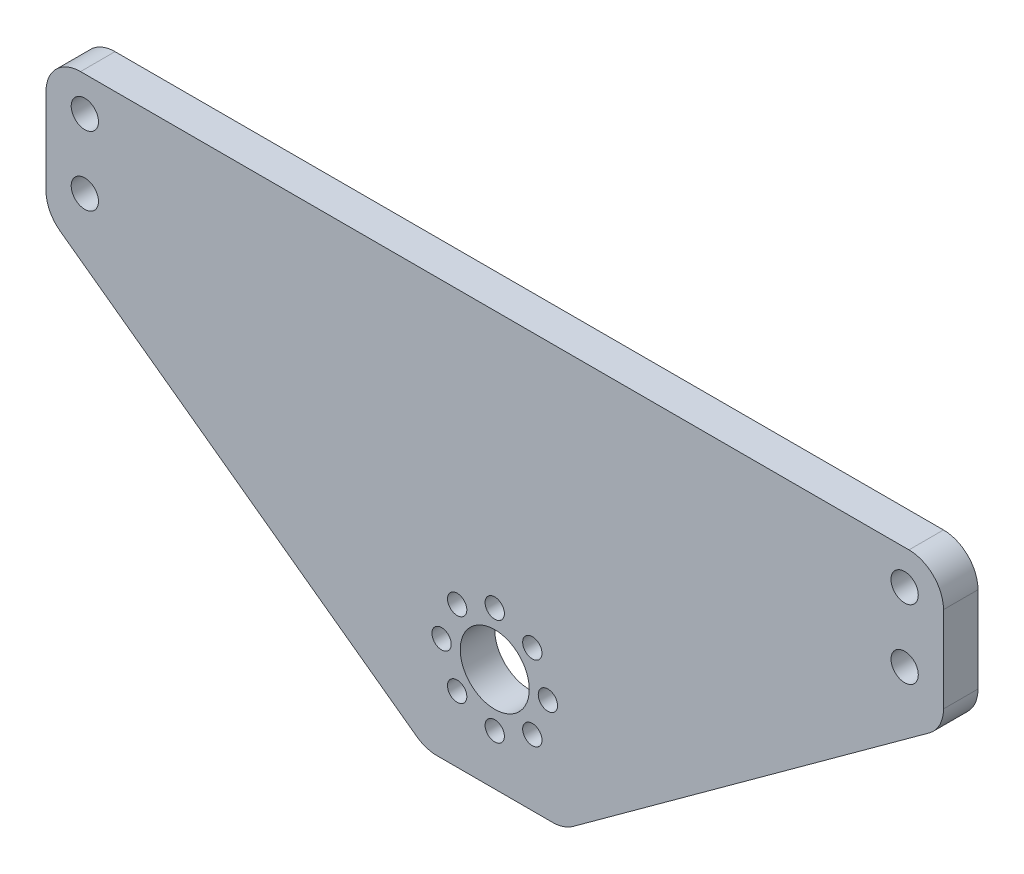
SolidWorks part; units mm, degrees
material "6061-T6 (SS)"
ref_plane "Front Plane" through (0, 0, 0) normal (0, 0, 1) x (1, 0, 0)
ref_plane "Top Plane" through (0, 0, 0) normal (0, 1, 0) x (1, 0, 0)
ref_plane "Right Plane" through (0, 0, 0) normal (1, 0, 0) x (0, 0, -1)
sketch "Sketch1" plane through (0, 0, 0) normal (0, 0, 1) x (1, 0, 0)
  line L1 (82.55, 38.1) -> (-82.55, 38.1)
  line L2 (82.55, 38.1) -> (82.55, -38.1)
  line L3 (82.55, -38.1) -> (-82.55, -38.1)
  line L4 (-82.55, 38.1) -> (-82.55, -38.1)
  line L5 (82.55, 38.1) -> (-82.55, -38.1) construction
  line L6 (82.55, -38.1) -> (-82.55, 38.1) construction
  circle A0 centre (0, -19.05) radius 6.35
  circle A1 centre (-75.4063, 31.75) radius 2.5083
  circle A2 centre (75.4062, 31.75) radius 2.5083
  circle A3 centre (75.4062, 19.05) radius 2.5083
  circle A4 centre (-75.4063, 19.05) radius 2.5083
  point P0 (0, 0)
  dimension "D3" = 12.7
  dimension "D4" = 75.4062
  dimension "D8" = 5.0165
  dimension "D9" = 5.0165
  dimension "D10" = 19.05
  dimension "D11" = 5.0165
  dimension "D12" = 5.0165
  dimension "D1" = 165.1
  dimension "D2" = 76.2
  dimension "D5" = 75.4062
  dimension "D6" = 50.8
  dimension "D7" = 50.8
  dimension "D13" = 75.4062
  dimension "D14" = 75.4063
  dimension "D15" = 12.7
  dimension "D16" = 12.7
extrude "Boss-Extrude1" add sketch "Sketch1" along normal blind 6.35
sketch "Sketch2" plane through (0, 0, 0) normal (0, 0, -1) x (-1, 0, 0)
  line L0 (12.7, -38.1) -> (82.55, 12.7)
  line L1 (82.55, -38.1) -> (-82.55, -38.1) construction
  line L2 (82.55, 38.1) -> (82.55, -38.1) construction
  line L3 (82.55, 12.7) -> (82.55, -38.1)
  line L4 (82.55, -38.1) -> (12.7, -38.1)
  line L5 (-82.55, -38.1) -> (-82.55, 12.7)
  line L6 (-82.55, -38.1) -> (-82.55, 38.1) construction
  line L7 (-82.55, 12.7) -> (-12.7, -38.1)
  line L8 (-12.7, -38.1) -> (-82.55, -38.1)
  dimension "D1" = 69.85
  dimension "D2" = 69.85
  dimension "D3" = 50.8
  dimension "D4" = 50.8
extrude "Cut-Extrude1" cut sketch "Sketch2" against normal blind 6.35
fillet "Fillet1" radius 6.35 6 edges at (-82.55, 38.1, 3.175) (82.55, 12.7, 3.175) (-82.55, 12.7, 3.175) (-12.7, -38.1, 3.175) (12.7, -38.1, 3.175) (82.55, 38.1, 3.175)
sketch "Sketch3" plane through (0, 0, 0) normal (0, 0, -1) x (-1, 0, 0)
  circle A0 centre (0, -9.271) radius 1.778
  circle A1 centre (0, -19.05) radius 6.35 construction
  dimension "D1" = 3.556
  dimension "D2" = 9.779
extrude "Cut-Extrude2" cut sketch "Sketch3" against normal blind 6.35
pattern_circular "CirPattern1" count 8 over 360 about axis through (0, -19.05, 0) along (0, 0, 1) of "Cut-Extrude2"
